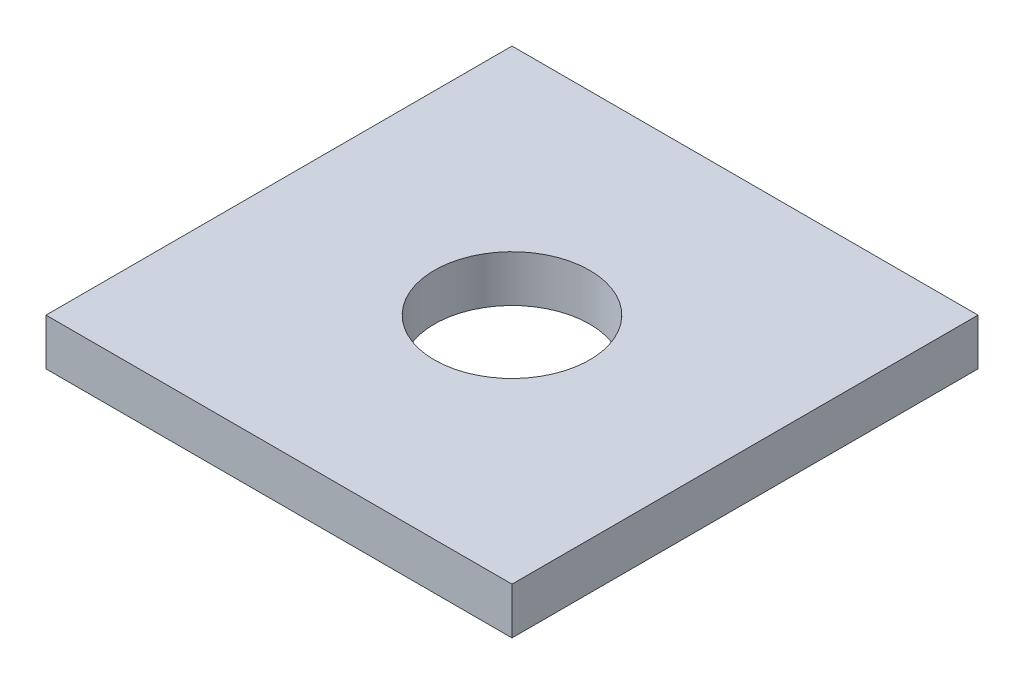
SolidWorks part; units mm, degrees
ref_plane "Front Plane" through (0, 0, 0) normal (0, 0, 1) x (1, 0, 0)
ref_plane "Top Plane" through (0, 0, 0) normal (0, 1, 0) x (1, 0, 0)
ref_plane "Right Plane" through (0, 0, 0) normal (1, 0, 0) x (0, 0, -1)
sketch "Sketch1" plane through (0, 0, 0) normal (0, 1, 0) x (1, 0, 0)
  line L0 (-15, 15) -> (15, -15) construction
  line L1 (-15, 15) -> (15, 15)
  line L2 (-15, 15) -> (-15, -15)
  line L3 (-15, -15) -> (15, -15)
  line L4 (15, 15) -> (15, -15)
  circle A0 centre (0, 0) radius 5
  dimension "D2" = 10
  dimension "D1" = 30
  dimension "D3" = 30
extrude "Boss-Extrude1" add sketch "Sketch1" along normal blind 3
